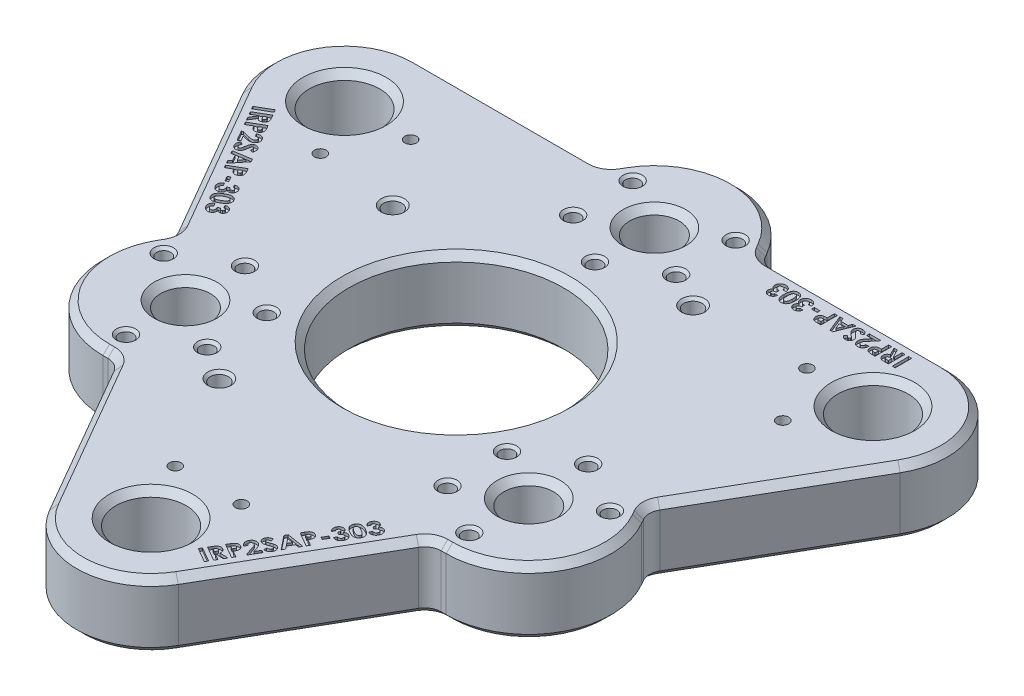
SolidWorks part; units mm, degrees
material "6061-T6 (SS)"
ref_plane "Front" through (0, 0, 0) normal (0, 0, 1) x (1, 0, 0)
ref_plane "Top" through (0, 0, 0) normal (0, 1, 0) x (1, 0, 0)
ref_plane "Right" through (0, 0, 0) normal (1, 0, 0) x (0, 0, -1)
sketch "Sketch1" plane through (0, 0, 0) normal (0, 1, 0) x (1, 0, 0)
  line L0 (-50.8, 43.6169) -> (50.8, 43.6169)
  line L1 (0, 43.6169) -> (0, 0) construction
  line L2 (63.1733, 22.1856) -> (12.3733, -65.8025)
  line L3 (0, 0) -> (-37.7733, -21.8084) construction
  line L4 (-12.3733, -65.8025) -> (-63.1733, 22.1856)
  line L5 (-37.7733, -21.8084) -> (37.7733, -21.8084) construction
  line L6 (37.7733, -21.8084) -> (0, 0) construction
  arc A0 (-50.8, 43.6169) -> (-63.1733, 22.1856) centre (-50.8, 29.3294) ccw
  arc A1 (63.1733, 22.1856) -> (50.8, 43.6169) centre (50.8, 29.3294) ccw
  arc A2 (-12.3733, -65.8025) -> (12.3733, -65.8025) centre (0, -58.6588) ccw
  dimension "D2" = 28.575
  dimension "D1" = 101.6
extrude "Boss-Extrude1" add sketch "Sketch1" along normal blind 12.7
hole_wizard "1/2 Clearance Hole1" positions "Sketch2" profile "Sketch3" hole size "1/2" standard "ANSI Inch" end condition through all
sketch "Sketch2" plane through (0, 12.7, 0) normal (0, 1, 0) x (1, 0, 0)
  point P0 (-50.8, 29.3294)
  point P3 (0, -58.6588)
  point P6 (50.8, 29.3294)
sketch "Sketch3" plane through (-50.8, 12.7, -29.3294) normal (1, 0, 0) x (0, 0, 1)
  line L0 (0, 0) -> (0, 12.7)
  line L1 (0, 12.7) -> (6.7462, 12.7)
  line L2 (6.7462, 12.7) -> (6.7462, 0)
  line L5 (6.7462, 0) -> (0, 0)
  line L11 (0, -6.35) -> (0, 107.95) construction
  dimension "Thru Hole Dia." = 13.4925
  dimension "Thru Hole Depth" = 12.7
sketch "Sketch6" plane through (0, 12.7, 0) normal (0, 1, 0) x (1, 0, 0)
  line L0 (0, 0) -> (-32.9956, -19.05) construction
  line L1 (0, 0) -> (32.9956, -19.05) construction
  line L2 (50.8, 29.3294) -> (32.9956, -19.05) construction
  line L3 (-15.1457, 43.6169) -> (-13.7482, 46.0375)
  line L4 (50.8, 43.6169) -> (-50.8, 43.6169) construction
  line L5 (13.7482, 46.0375) -> (15.1457, 43.6169)
  line L6 (15.1457, 43.6169) -> (-15.1457, 43.6169)
  line L7 (0, 38.1) -> (0, 0) construction
  line L14 (32.9956, -34.925) -> (30.2005, -34.925)
  line L15 (45.3462, -8.6919) -> (46.7437, -11.1125)
  line L16 (-46.7437, -11.1125) -> (-45.3462, -8.6919)
  line L17 (-30.2005, -34.925) -> (-32.9956, -34.925)
  line L18 (-45.3462, -8.6919) -> (-30.2005, -34.925)
  line L19 (45.3462, -8.6919) -> (30.2005, -34.925)
  line L20 (12.3733, -65.8025) -> (63.1733, 22.1856) construction
  line L21 (-63.1733, 22.1856) -> (-12.3733, -65.8025) construction
  line L22 (32.9956, -19.05) -> (0, -58.6588) construction
  arc A3 (-13.7482, 46.0375) -> (13.7482, 46.0375) centre (0, 38.1) cw
  arc A6 (46.7437, -11.1125) -> (32.9956, -34.925) centre (32.9956, -19.05) cw
  arc A7 (-32.9956, -34.925) -> (-46.7437, -11.1125) centre (-32.9956, -19.05) cw
  point P21 (0, 0)
  dimension "D1" = 15.875
  dimension "D2" = 60
  dimension "D4" = 38.1
  dimension "D3" = 3
extrude "Boss-Extrude2" add sketch "Sketch6" against normal blind 12.7
fillet "Fillet1" radius 3.175 6 edges at (30.2005, 6.35, 34.925) (45.3462, 6.35, 8.6919) (15.1457, 6.35, -43.6169) (-15.1457, 6.35, -43.6169) (-30.2005, 6.35, 34.925) (-45.3462, 6.35, 8.6919)
chamfer "Chamfer1" distance 1.27 angle 45 54 edges at (63.1733, 0, -36.4731) (63.1733, 12.7, -36.4731) (33.8894, 0, -43.6169) (33.8894, 12.7, -43.6169) (-33.8894, 12.7, -43.6169) (-33.8894, 0, -43.6169) (-63.1733, 0, -36.4731) (-63.1733, 12.7, -36.4731) (-54.718, 0, -7.5406) (-54.718, 12.7, -7.5406) (-20.8286, 12.7, 51.1575) (-20.8286, 0, 51.1575) (0, 0, 72.9463) (0, 12.7, 72.9463) (20.8286, 0, 51.1575) (20.8286, 12.7, 51.1575) (54.718, 12.7, -7.5406) (54.718, 0, -7.5406) (50.8, 0, -22.5832) (50.8, 12.7, -22.5832) (0, 0, 65.405) (0, 12.7, 65.405) (-50.8, 0, -22.5832) (-50.8, 12.7, -22.5832) (0, 12.7, -53.975) (0, 0, -53.975) (13.9887, 12.7, -45.6209) (13.9887, 0, -45.6209) (15.3913, 0, -44.0423) (15.3913, 12.7, -44.0423) (45.8374, 0, 8.6919) (45.8374, 12.7, 8.6919) (46.5032, 0, 10.6959) (46.5032, 12.7, 10.6959) (46.7437, 12.7, 26.9875) (46.7437, 0, 26.9875) (32.5146, 12.7, 34.925) (32.5146, 0, 34.925) (30.4461, 0, 35.3504) (30.4461, 12.7, 35.3504) (-30.4461, 0, 35.3504) (-30.4461, 12.7, 35.3504) (-32.5146, 0, 34.925) (-32.5146, 12.7, 34.925) (-46.7437, 12.7, 26.9875) (-46.7437, 0, 26.9875) (-46.5032, 12.7, 10.6959) (-46.5032, 0, 10.6959) (-45.8374, 0, 8.6919) (-45.8374, 12.7, 8.6919) (-15.3913, 0, -44.0423) (-15.3913, 12.7, -44.0423) (-13.9887, 0, -45.6209) (-13.9887, 12.7, -45.6209)
hole_wizard "#4-40 Tapped Hole1" positions "Sketch7" profile "Sketch8" tap size "#4-40" standard "ANSI Inch"
sketch "Sketch7" plane through (-37.7733, 0, 21.8084) normal (-0.866, 0, 0.5) x (0.5, 0, 0.866)
  line L0 (-50.8, 6.35) -> (-44.45, 6.35) construction
  line L1 (-50.8, 11.43) -> (-50.8, 1.27) construction
  line L2 (-44.45, 6.35) -> (0, 6.35) construction
  line L8 (44.45, 6.35) -> (50.8, 6.35) construction
  line L9 (50.8, 11.43) -> (50.8, 1.27) construction
  line L13 (0, 6.35) -> (44.45, 6.35) construction
  line L15 (12.6483, 12.7) -> (-12.6483, 12.7) construction
  point P0 (-44.45, 6.35)
  point P2 (44.45, 6.35)
  point P41 (0, 12.7)
  dimension "D1" = 44.45
sketch "Sketch8" plane through (-59.9983, 6.35, -16.6864) normal (0, 1, 0) x (0.5, 0, 0.866)
  line L0 (0, 0) -> (0, 8.6167)
  line L1 (0, 8.6167) -> (1.1303, 7.9375)
  line L2 (1.1303, 7.9375) -> (1.1303, 0)
  line L5 (1.1303, 0) -> (0, 0)
  line L10 (0, 8.6167) -> (-1.1303, 7.9375) construction
  line L11 (0, -6.35) -> (0, 107.95) construction
  dimension "Tap Drill Dia." = 2.2606
  dimension "Tap Drill Depth" = 7.9375
  dimension "Drill Angle" = 118
cosmetic thread "Hole Thread4" parameters "D1"=6.35, "D2"=2.8448
cosmetic thread "Hole Thread5" parameters "D1"=6.35, "D2"=2.8448
ref_plane "Plane1" through (0, 0, 0) normal (-0.5, 0, 0.866) x (0.866, 0, 0.5)
mirror "Mirror1" about plane through (0, 0, 0) normal (-0.5, 0, 0.866) of "#4-40 Tapped Hole1"
cosmetic thread "Hole Thread6" parameters "D1"=6.35, "D2"=2.8448
cosmetic thread "Hole Thread7" parameters "D1"=6.35, "D2"=2.8448
hole_wizard "#6-32 Tapped Hole2" positions "Sketch9" profile "Sketch10" tap size "#6-32" standard "ANSI Inch" end condition through all
sketch "Sketch9" plane through (0, 12.7, 0) normal (0, 1, 0) x (1, 0, 0)
  line L1 (0, 49.53) -> (-9.8987, 43.815) construction
  line L2 (-9.8987, 43.815) -> (-9.8987, 32.385) construction
  line L3 (-9.8987, 32.385) -> (0, 26.67) construction
  line L4 (0, 26.67) -> (9.8987, 32.385) construction
  line L5 (9.8987, 32.385) -> (9.8987, 43.815) construction
  line L6 (9.8987, 43.815) -> (0, 49.53) construction
  line L8 (42.8942, -24.765) -> (42.8942, -13.335) construction
  line L9 (42.8942, -13.335) -> (32.9956, -7.62) construction
  line L10 (32.9956, -7.62) -> (23.0969, -13.335) construction
  line L11 (23.0969, -13.335) -> (23.0969, -24.765) construction
  line L12 (23.0969, -24.765) -> (32.9956, -30.48) construction
  line L13 (32.9956, -30.48) -> (42.8942, -24.765) construction
  line L15 (-42.8942, -24.765) -> (-32.9956, -30.48) construction
  line L16 (-32.9956, -30.48) -> (-23.0969, -24.765) construction
  line L17 (-23.0969, -24.765) -> (-23.0969, -13.335) construction
  line L18 (-23.0969, -13.335) -> (-32.9956, -7.62) construction
  line L19 (-32.9956, -7.62) -> (-42.8942, -13.335) construction
  line L20 (-42.8942, -13.335) -> (-42.8942, -24.765) construction
  line L21 (-32.9956, -19.05) -> (-23.0969, -13.335) construction
  line L24 (32.9956, -19.05) -> (23.0969, -13.335) construction
  circle A1 centre (0, 38.1) radius 9.8987 construction
  circle A2 centre (32.9956, -19.05) radius 9.8987 construction
  circle A3 centre (-32.9956, -19.05) radius 9.8987 construction
  circle A4 centre (0, 38.1) radius 11.43 construction
  point P6 (-9.8987, 43.815)
  point P7 (-9.8987, 32.385)
  point P8 (0, 26.67)
  point P9 (9.8987, 32.385)
  point P10 (9.8987, 43.815)
  point P16 (42.8942, -13.335)
  point P17 (32.9956, -7.62)
  point P18 (23.0969, -13.335)
  point P19 (23.0969, -24.765)
  point P20 (32.9956, -30.48)
  point P26 (-32.9956, -30.48)
  point P27 (-23.0969, -24.765)
  point P28 (-23.0969, -13.335)
  point P29 (-32.9956, -7.62)
  point P30 (-42.8942, -13.335)
  dimension "D1" = 22.86
sketch "Sketch10" plane through (-42.8942, 12.7, 13.335) normal (1, 0, 0) x (0, 0, 1)
  line L0 (0, 0) -> (0, 12.7)
  line L1 (0, 12.7) -> (1.3525, 12.7)
  line L2 (1.3525, 12.7) -> (1.3525, 0)
  line L5 (1.3525, 0) -> (0, 0)
  line L11 (0, -6.35) -> (0, 107.95) construction
  dimension "Thru Tap Drill Dia." = 2.7051
  dimension "Thru Tap Drill Depth" = 12.7
cosmetic thread "Hole Thread8" parameters "D2"=3.5052
cosmetic thread "Hole Thread9" parameters "D2"=3.5052
cosmetic thread "Hole Thread10" parameters "D2"=3.5052
cosmetic thread "Hole Thread11" parameters "D2"=3.5052
cosmetic thread "Hole Thread12" parameters "D2"=3.5052
cosmetic thread "Hole Thread13" parameters "D2"=3.5052
cosmetic thread "Hole Thread14" parameters "D2"=3.5052
cosmetic thread "Hole Thread15" parameters "D2"=3.5052
cosmetic thread "Hole Thread16" parameters "D2"=3.5052
cosmetic thread "Hole Thread23" parameters "D2"=3.5052
cosmetic thread "Hole Thread24" parameters "D2"=3.5052
cosmetic thread "Hole Thread25" parameters "D2"=3.5052
cosmetic thread "Hole Thread26" parameters "D2"=3.5052
cosmetic thread "Hole Thread27" parameters "D2"=3.5052
cosmetic thread "Hole Thread28" parameters "D2"=3.5052
sketch "Sketch11" plane through (0, 12.7, 0) normal (0, 1, 0) x (1, 0, 0)
  circle A0 centre (0, 0) radius 20.6375
  dimension "D1" = 41.275
extrude "Cut-Extrude1" cut sketch "Sketch11" against normal through all
sketch "Sketch14" plane through (0, 0, 0) normal (0, -1, 0) x (-1, 0, 0)
  circle A0 centre (32.9956, -19.05) radius 4.7625
  circle A1 centre (-32.9956, -19.05) radius 4.7625
  circle A2 centre (0, 38.1) radius 4.7625
  arc A3 (12.6483, 45.4025) -> (-12.6483, 45.4025) centre (0, 38.1) ccw construction
  arc A4 (-45.6439, -11.7475) -> (-32.9956, -33.655) centre (-32.9956, -19.05) ccw construction
  arc A5 (32.9956, -33.655) -> (45.6439, -11.7475) centre (32.9956, -19.05) ccw construction
  dimension "D1" = 9.525
extrude "Cut-Extrude2" cut sketch "Sketch14" against normal through all
hole_wizard "#8-32 Tapped Hole1" positions "Sketch15" profile "Sketch16" tap size "#8-32" standard "ANSI Inch" end condition through all
sketch "Sketch15" plane through (0, 12.7, 0) normal (0, 1, 0) x (1, 0, 0)
  line L0 (28.8687, -16.6674) -> (-16.6674, -28.8687) construction
  line L1 (-16.6674, -28.8687) -> (-28.8687, 16.6674) construction
  line L2 (-28.8687, 16.6674) -> (16.6674, 28.8687) construction
  line L3 (16.6674, 28.8687) -> (28.8687, -16.6674) construction
  line L5 (28.8687, -16.6674) -> (0, 0) construction
  line L6 (0, 0) -> (-28.8687, 16.6674) construction
  line L7 (-28.8687, 16.6674) -> (-50.8, 29.3294) construction
  circle A0 centre (-50.8, 29.3294) radius 8.0162 construction
  point P2 (-16.6674, -28.8687)
  point P4 (-28.8687, 16.6674)
  point P6 (16.6674, 28.8687)
  dimension "D1" = 47.1424
sketch "Sketch16" plane through (-16.6674, 12.7, 28.8687) normal (1, 0, 0) x (0, 0, 1)
  line L0 (0, 0) -> (0, 12.7)
  line L1 (0, 12.7) -> (1.7272, 12.7)
  line L2 (1.7272, 12.7) -> (1.7272, 0)
  line L5 (1.7272, 0) -> (0, 0)
  line L11 (0, -6.35) -> (0, 107.95) construction
  dimension "Thru Tap Drill Dia." = 3.4544
  dimension "Thru Tap Drill Depth" = 12.7
cosmetic thread "Hole Thread29" parameters "D2"=4.1656
cosmetic thread "Hole Thread30" parameters "D2"=4.1656
cosmetic thread "Hole Thread31" parameters "D2"=4.1656
chamfer "Chamfer3" distance 0.508 angle 45 36 edges at (9.8987, 0, -42.4625) (9.8987, 12.7, -42.4625) (-9.8987, 0, -42.4624) (-9.8987, 12.7, -42.4624) (-9.8987, 0, -31.0325) (-9.8987, 12.7, -31.0325) (9.8987, 0, -31.0325) (9.8987, 12.7, -31.0325) (0, 0, -25.3175) (0, 12.7, -25.3175) (32.9956, 0, 8.9725) (32.9956, 12.7, 8.9725) (42.8942, 0, 14.6875) (42.8942, 12.7, 14.6875) (32.9956, 0, 31.8325) (32.9956, 12.7, 31.8325) (23.0969, 0, 26.1176) (23.0969, 12.7, 26.1176) (23.0969, 0, 14.6875) (23.0969, 12.7, 14.6875) (-23.0969, 0, 14.6876) (-23.0969, 12.7, 14.6876) (-32.9956, 0, 8.9726) (-32.9956, 12.7, 8.9726) (-23.0969, 0, 26.1176) (-23.0969, 12.7, 26.1176) (-32.9956, 0, 31.8326) (-32.9956, 12.7, 31.8326) (-42.8942, 0, 14.6876) (-42.8942, 12.7, 14.6876) (-16.6674, 0, 30.5959) (-16.6674, 12.7, 30.5959) (16.6674, 0, -27.1415) (16.6674, 12.7, -27.1415) (-28.8687, 0, -14.9402) (-28.8687, 12.7, -14.9402)
chamfer "Chamfer2" distance 1.27 angle 45 8 edges at (0, 0, 20.6375) (0, 12.7, 20.6375) (-32.9956, 12.7, 14.2875) (-32.9956, 0, 14.2875) (32.9956, 12.7, 14.2875) (32.9956, 0, 14.2875) (0, 12.7, -42.8625) (0, 0, -42.8625)
hole_wizard "#4-40 Tapped Hole2" positions "Sketch17" profile "Sketch18" tap size "#4-40" standard "ANSI Inch"
sketch "Sketch17" plane through (0, 12.7, 0) normal (0, 1, 0) x (1, 0, 0)
  line L0 (-6.35, -47.6603) -> (6.35, -47.6603) construction
  line L1 (6.35, -47.6603) -> (44.45, 18.3309) construction
  line L2 (44.45, 18.3309) -> (38.1, 29.3294) construction
  line L3 (38.1, 29.3294) -> (-38.1, 29.3294) construction
  line L4 (-38.1, 29.3294) -> (-44.45, 18.3309) construction
  line L6 (38.1, 29.3294) -> (50.8, 29.3294) construction
  line L7 (50.8, 29.3294) -> (44.45, 18.3309) construction
  line L9 (6.35, -47.6603) -> (0, -58.6588) construction
  line L10 (0, -58.6588) -> (-6.35, -47.6603) construction
  line L12 (-38.1, 29.3294) -> (-50.8, 29.3294) construction
  line L13 (-50.8, 29.3294) -> (-44.45, 18.3309) construction
  line L15 (-44.45, 18.3309) -> (-6.35, -47.6603) construction
  circle A0 centre (50.8, 29.3294) radius 6.7462 construction
  circle A1 centre (0, -58.6588) radius 6.7462 construction
  circle A2 centre (-50.8, 29.3294) radius 6.7462 construction
  point P0 (38.1, 29.3294)
  point P2 (44.45, 18.3309)
  point P4 (-38.1, 29.3294)
  point P6 (-44.45, 18.3309)
  point P8 (-6.35, -47.6603)
  point P10 (6.35, -47.6603)
  dimension "D1" = 12.7
sketch "Sketch18" plane through (38.1, 12.7, -29.3294) normal (1, 0, 0) x (0, 0, 1)
  line L0 (0, 0) -> (0, 8.2738)
  line L1 (0, 8.2738) -> (1.1303, 7.5946)
  line L2 (1.1303, 7.5946) -> (1.1303, 0)
  line L5 (1.1303, 0) -> (0, 0)
  line L10 (0, 8.2738) -> (-1.1303, 7.5946) construction
  line L11 (0, -6.35) -> (0, 107.95) construction
  dimension "Tap Drill Dia." = 2.2606
  dimension "Tap Drill Depth" = 7.5946
  dimension "Drill Angle" = 118
cosmetic thread "Hole Thread32" parameters "D1"=5.6896, "D2"=2.8448
cosmetic thread "Hole Thread33" parameters "D1"=5.6896, "D2"=2.8448
cosmetic thread "Hole Thread34" parameters "D1"=5.6896, "D2"=2.8448
cosmetic thread "Hole Thread35" parameters "D1"=5.6896, "D2"=2.8448
cosmetic thread "Hole Thread36" parameters "D1"=5.6896, "D2"=2.8448
cosmetic thread "Hole Thread37" parameters "D1"=5.6896, "D2"=2.8448
sketch "Sketch19" plane through (0, 12.7, 0) normal (0, 1, 0) x (1, 0, 0)
  line L0 (-62.0433, 25.3084) -> (-42.9933, -7.6872) construction
  line L1 (-62.0735, 22.8206) -> (-45.1629, -6.4694) construction
  line L2 (-53.6182, 8.1756) -> (-52.5183, 8.8106) construction
  line L3 (52.9394, 41.0769) -> (14.8394, 41.0769) construction
  line L4 (9.1039, -66.3853) -> (28.1539, -33.3897) construction
  line L5 (19.7288, -50.5225) -> (18.6289, -49.8875) construction
  line L6 (11.2735, -65.1675) -> (28.1841, -35.8775) construction
  text T0 "<b>IRP2SAP-303</b>"
  text T1 "<b>IRP2SAP-303</b>"
  text T2 "<b>IRP2SAP-303</b>"
  point P8 (0, 0)
  point P15 (0, 0)
  dimension "D1" = 1.27
  dimension "D2" = 38.1
  dimension "D4" = 1.27
  dimension "D3" = 3
extrude "Cut-Extrude3" cut sketch "Sketch19" against normal blind 0.508
